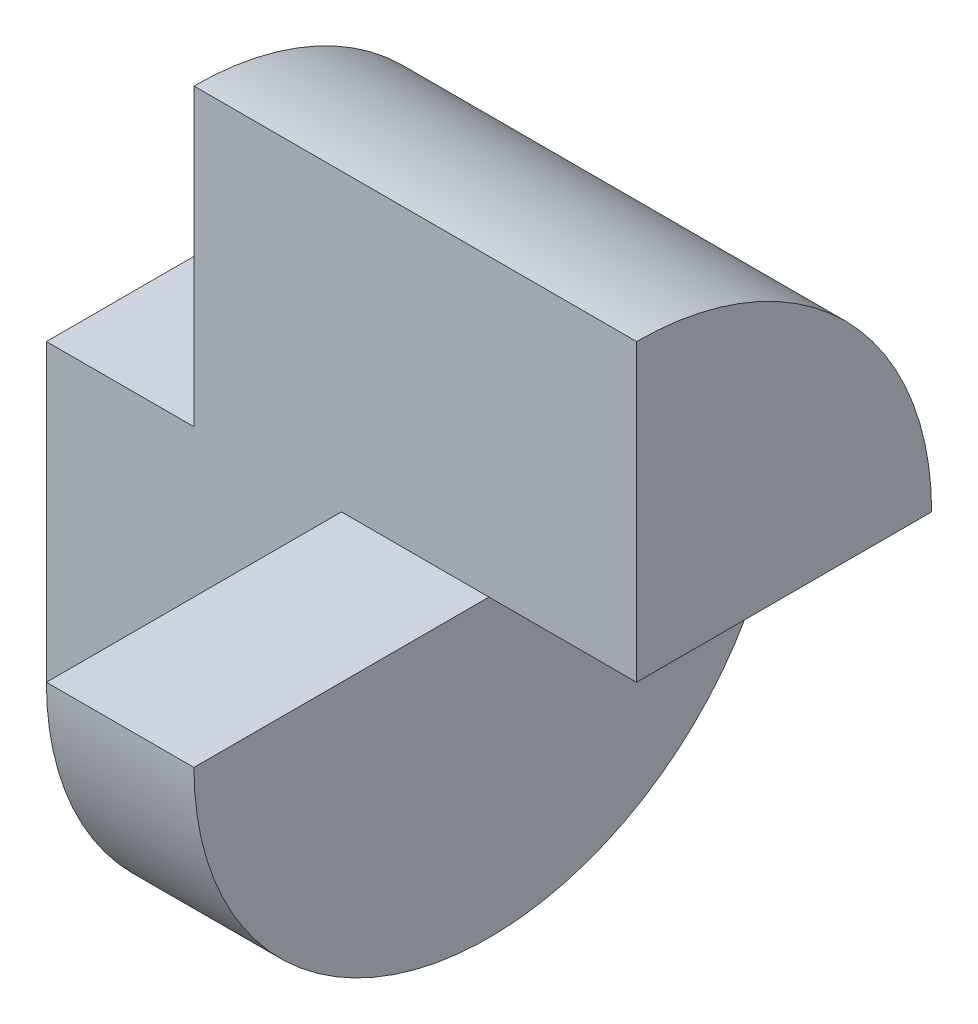
SolidWorks part; units mm, degrees
ref_plane "Front Plane" through (0, 0, 0) normal (0, 0, 1) x (1, 0, 0)
ref_plane "Top Plane" through (0, 0, 0) normal (0, 1, 0) x (1, 0, 0)
ref_plane "Right Plane" through (0, 0, 0) normal (1, 0, 0) x (0, 0, -1)
sketch "Sketch1" plane through (0, 0, 0) normal (0, 0, 1) x (1, 0, 0)
  line L1 (0, 0) -> (40, 0)
  line L2 (0, 0) -> (0, 40)
  line L3 (0, 40) -> (40, 40)
  line L4 (40, 0) -> (40, 40)
  dimension "D1" = 40
  dimension "D2" = 40
extrude "Boss-Extrude1" add sketch "Sketch1" along normal blind 40
sketch "Sketch2" plane through (0, 0, 40) normal (0, 0, 1) x (1, 0, 0)
  line L1 (0, 40) -> (10, 40)
  line L2 (0, 40) -> (0, 20)
  line L3 (0, 20) -> (10, 20)
  line L4 (10, 40) -> (10, 20)
  line L5 (40, 0) -> (30, 0)
  line L6 (40, 0) -> (40, 20)
  line L7 (40, 20) -> (30, 20)
  line L8 (30, 0) -> (30, 20)
  dimension "D1" = 10
  dimension "D2" = 10
  dimension "D3" = 20
  dimension "D4" = 20
extrude "Cut-Extrude1" cut sketch "Sketch2" against normal blind 40
sketch "Sketch3" plane through (10, 0, 0) normal (-1, 0, 0) x (0, 0, 1)
  line L0 (0, 20) -> (40, 20) construction
  line L1 (40, 40) -> (20, 40)
  line L2 (40, 40) -> (40, 20)
  line L3 (40, 20) -> (20, 20)
  line L4 (20, 40) -> (20, 20)
extrude "Cut-Extrude2" cut sketch "Sketch3" against normal blind 40
sketch "Sketch4" plane through (10, 0, 0) normal (-1, 0, 0) x (0, 0, 1)
  line L0 (0, 20) -> (20, 20) construction
  line L1 (0, 20) -> (0, 40)
  line L2 (0, 40) -> (20, 40)
  arc A0 (20, 40) -> (0, 20) centre (20, 20) ccw
extrude "Cut-Extrude3" cut sketch "Sketch4" against normal blind 40
sketch "Sketch5" plane through (0, 0, 0) normal (-1, 0, 0) x (0, 0, 1)
  line L0 (0, 20) -> (40, 20) construction
  line L1 (0, 20) -> (0, 0)
  line L2 (0, 0) -> (40, 0)
  line L3 (40, 0) -> (40, 20)
  line L4 (40, 20) -> (40.1166, 21.1637)
  arc A0 (40, 20) -> (0, 20) centre (20, 20) cw
  line M1 (40, 0) -> (40, 20)
  line M3 (0, 20) -> (0, 0)
  line M4 (0, 0) -> (40, 0)
extrude "Cut-Extrude4" cut sketch "Sketch5" against normal blind 40 contours A0 M4 M3 | A0 L2 M1
sketch "Sketch6" plane through (0, 0, 0) normal (-1, 0, 0) x (0, 0, 1)
  line L0 (0, 20) -> (40, 20) construction
  line L1 (20, 0) -> (20, 20)
  line L2 (20, 20) -> (40, 20)
  arc A0 (40, 20) -> (20, 0) centre (20, 20) cw
extrude "Cut-Extrude5" cut sketch "Sketch6" against normal blind 20
